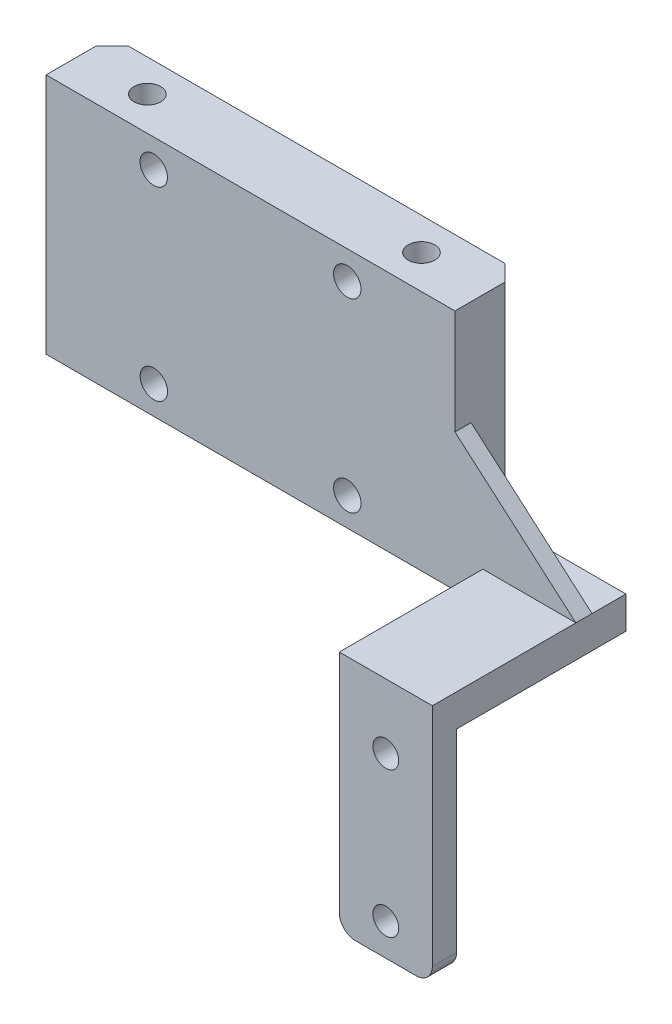
SolidWorks part; units mm, degrees
ref_plane "前视基准面" through (0, 0, 0) normal (0, 0, 1) x (1, 0, 0)
ref_plane "上视基准面" through (0, 0, 0) normal (0, 1, 0) x (1, 0, 0)
ref_plane "右视基准面" through (0, 0, 0) normal (1, 0, 0) x (0, 0, -1)
sketch "草图1" plane through (0, 0, 0) normal (0, 0, 1) x (1, 0, 0)
  line L1 (-23.8452, 10.7072) -> (26.8548, 10.7072)
  line L2 (-23.8452, 10.7072) -> (-23.8452, -19.2928)
  line L3 (-23.8452, -19.2928) -> (26.8548, -19.2928)
  line L4 (26.8548, 10.7072) -> (26.8548, -19.2928)
  dimension "D1" = 50.7
  dimension "D2" = 30
extrude "凸台-拉伸1" add sketch "草图1" along normal blind 8.2
sketch "草图2" plane through (0, 10.7072, 0) normal (0, 1, 0) x (1, 0, 0)
  line L5 (-23.8452, -8.2) -> (-23.8452, 0) construction
  line L6 (-21.8452, 0) -> (-23.8452, -2)
  line L7 (-23.8452, -2) -> (-23.8452, 0)
  line L8 (-23.8452, 0) -> (-21.8452, 0)
  line L9 (24.8548, 0) -> (26.8548, -2)
  line L10 (26.8548, -2) -> (26.8548, 0)
  line L11 (26.8548, 0) -> (24.8548, 0)
extrude "切除-拉伸1" cut sketch "草图2" against normal through all
sketch "草图3" plane through (0, 0, 0) normal (0, 0, -1) x (-1, 0, 0)
  line L0 (31.1482, -4.2928) -> (-34.5046, -4.2928)
  line L1 (-1.5048, 14.1143) -> (-1.5048, -24.1447)
  line L2 (-33.6955, -15.7928) -> (30.108, -15.7928)
  line L3 (30.108, 7.2072) -> (-33.6955, 7.2072)
  line L4 (-13.5048, 13.4207) -> (-13.5048, -24.1447)
  line L5 (10.4952, -24.1447) -> (10.4952, 15.3857)
  dimension "D1" = 12
  dimension "D2" = 12
  dimension "D3" = 11.5
  dimension "D4" = 11.5
hole_wizard "M3 平头机械螺钉的锥形沉头孔1" positions "3D草图1" profile "草图4" countersink size "M3" standard "ANSI Metric" end condition through all
sketch3d "3D草图1"
  line L0 (33.6955, -15.7928, 0) -> (-30.108, -15.7928, 0) construction
  line L1 (13.5048, 13.4207, 0) -> (13.5048, -24.1447, 0) construction
  line L2 (-30.108, 7.2072, 0) -> (33.6955, 7.2072, 0) construction
  line L3 (-10.4952, -24.1447, 0) -> (-10.4952, 15.3857, 0) construction
  point P0 (-10.4861, -15.7928, 0)
  point P4 (13.5048, -15.7928, 0)
  point P8 (13.5048, 7.2072, 0)
  point P12 (-10.4952, 7.2072, 0)
sketch "草图4" plane through (-10.4861, -15.7928, 0) normal (1, 0, 0) x (0, 1, 0)
  line L0 (0, 0) -> (0, 8.2)
  line L1 (0, 8.2) -> (1.7, 8.2)
  line L2 (1.7, 8.2) -> (1.7, 1.45)
  line L3 (1.7, 1.45) -> (3.15, 0)
  line L5 (3.15, 0) -> (0, 0)
  line L6 (-1.7, 1.45) -> (-3.15, 0) construction
  line L11 (0, -6.35) -> (0, 107.95) construction
  dimension "通孔孔直径" = 3.4
  dimension "通孔孔深度" = 8.2
  dimension "近端锥形沉头孔直径" = 6.3
  dimension "近端锥形沉头孔角度" = 90
sketch "草图5" plane through (0, -19.2928, 0) normal (0, -1, 0) x (1, 0, 0)
  circle A0 centre (-15.4952, 4) radius 1.65
  circle A1 centre (18.5048, 4) radius 1.65
  dimension "D4" = 3.3
  dimension "D5" = 3.3
extrude "切除-拉伸2" cut sketch "草图5" against normal through all
sketch "草图6" plane through (26.8548, 0, 0) normal (1, 0, 0) x (0, 0, -1)
  line L0 (-11.9727, -14.2928) -> (-0.3594, -14.2928)
  line L1 (-8.2, -19.2928) -> (-2, -19.2928) construction
  line L2 (-8.2025, -14.2928) -> (-8.2, -19.2928)
  line L3 (-8.2, -19.2928) -> (-2, -19.2928)
  line L4 (-2, -19.2928) -> (-2, -14.2928)
  line L5 (-2, -19.2928) -> (-2, 10.7072) construction
  line L6 (-2, -14.2928) -> (-8.2025, -14.2928)
  line M2 (-8.2, -19.2928) -> (-2, -19.2928)
  line M3 (-2, -19.2928) -> (-2, 10.7072)
  line M5 (-8.2, 10.7072) -> (-8.2, -19.2928)
  dimension "D1" = 5
extrude "凸台-拉伸2" add sketch "草图6" along normal blind 15 contours L0 M5 M2 M3
sketch "草图7" plane through (0, 0, 8.2) normal (0, 0, 1) x (1, 0, 0)
  line L0 (30.3148, -25.9726) -> (30.3148, -6.4539)
  line L1 (41.8548, -14.2928) -> (41.8548, -19.2928) construction
  line L2 (30.3148, -19.2928) -> (41.8548, -19.2928)
  line L3 (-23.8452, -19.2928) -> (41.8548, -19.2928) construction
  line L4 (41.8548, -19.2928) -> (41.8548, -14.2928)
  line L5 (41.8548, -14.2928) -> (30.3148, -14.2928)
  line L6 (41.8548, -14.2928) -> (26.8548, -14.2928) construction
  line L7 (30.3148, -14.2928) -> (30.3148, -19.2928)
  dimension "D1" = 11.54
sketch "草图9" plane through (0, 0, 8.2) normal (0, 0, 1) x (1, 0, 0)
  line L0 (30.3148, -19.2928) -> (41.8548, -19.2928)
  line L1 (41.8548, -19.2928) -> (41.8548, -14.2928)
  line L2 (41.8548, -14.2928) -> (30.3148, -14.2928)
  line L3 (30.3148, -14.2928) -> (30.3148, -19.2928)
extrude "凸台-拉伸7" add sketch "草图9" along normal blind 17.8
sketch "草图10" plane through (0, -19.2928, 0) normal (0, -1, 0) x (1, 0, 0)
  line L0 (24.1352, 23) -> (58.3804, 23)
  line L1 (30.3148, 26) -> (41.8548, 26) construction
  line L2 (30.3148, 23) -> (30.3148, 26)
  line L3 (30.3148, 26) -> (30.3148, 8.2) construction
  line L4 (30.3148, 26) -> (41.8548, 26)
  line L5 (41.8548, 26) -> (41.8548, 23)
  line L6 (41.8548, 26) -> (41.8548, 2) construction
  line L7 (41.8548, 23) -> (30.3148, 23)
  line M9 (41.8548, 2) -> (41.8548, 26)
  line M10 (41.8548, 26) -> (30.3148, 26)
  line M11 (30.3148, 26) -> (30.3148, 8.2)
  dimension "D1" = 3
extrude "凸台-拉伸8" add sketch "草图10" along normal blind 26 contours L0 M11 M9 M10
sketch "草图11" plane through (0, 0, 23) normal (0, 0, -1) x (-1, 0, 0)
  circle A0 centre (-36.0848, -41.2928) radius 1.6
  circle A1 centre (-36.0848, -23.2928) radius 1.6
  dimension "D3" = 3.2
  dimension "D4" = 3.2
extrude "切除-拉伸3" cut sketch "草图11" against normal through all
sketch "草图15" plane through (30.3148, 0, 0) normal (-1, 0, 0) x (0, 0, 1)
  line L0 (23, -24.8832) -> (4.6479, -19.2928)
  line L1 (23, -45.2928) -> (23, -19.2928) construction
  line L2 (4.6479, -19.2928) -> (23, -19.2928)
  line L3 (23, -19.2928) -> (23, -24.8832)
  point P4 (23, -24.8832)
extrude "凸台-拉伸10" add sketch "草图15" against normal blind 1
fillet "圆角1" radius 2 2 edges at (30.3148, -45.2928, 24.5) (41.8548, -45.2928, 24.5)
sketch "草图17" plane through (0, -14.2928, 0) normal (0, 1, 0) x (1, 0, 0)
  line L0 (26.8548, -8.2) -> (30.3148, -8.2)
  line L1 (30.3148, -8.2) -> (30.3148, -26)
  line L2 (30.3148, -26) -> (41.8548, -26)
  line L3 (41.8548, -26) -> (41.8548, -2)
  line L4 (41.8548, -2) -> (26.8548, -2)
  line L5 (26.8548, -2) -> (26.8548, -8.2)
extrude "切除-拉伸4" cut sketch "草图17" against normal blind 1
sketch "草图18" plane through (0, 0, 8.2) normal (0, 0, 1) x (1, 0, 0)
  line L0 (30.3148, -15.2928) -> (48.1781, -15.2928)
  line L1 (26.8548, -15.2928) -> (26.8548, -2.2928)
  line L2 (26.8548, -15.2928) -> (26.8548, 10.7072) construction
  line L3 (26.8548, -2.2928) -> (41.8543, -15.2928)
  line L4 (26.8548, -2.2928) -> (26.8548, -15.2928)
  line L5 (41.8543, -15.2928) -> (26.8548, -2.2928)
  line M1 (30.3148, -15.2928) -> (26.8548, -15.2928)
  line M2 (26.8548, -15.2928) -> (26.8548, 10.7072)
extrude "凸台-拉伸11" add sketch "草图18" against normal blind 2 contours L3 L0 M2 M1
